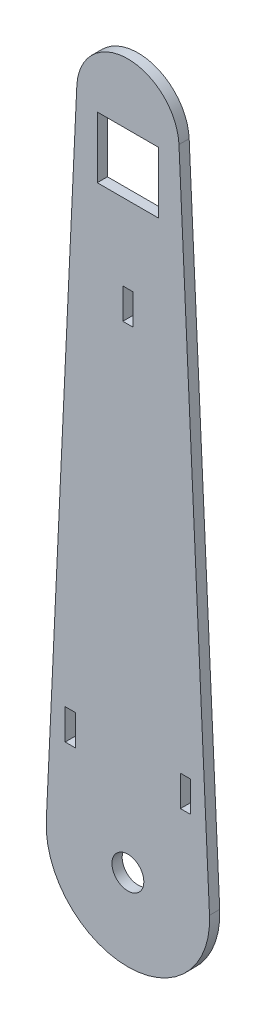
SolidWorks part; units mm, degrees
ref_plane "Front Plane" through (0, 0, 0) normal (0, 0, 1) x (1, 0, 0)
ref_plane "Top Plane" through (0, 0, 0) normal (0, 1, 0) x (1, 0, 0)
ref_plane "Right Plane" through (0, 0, 0) normal (1, 0, 0) x (0, 0, -1)
sketch "Sketch1" plane through (0, 0, 0) normal (0, 0, 1) x (1, 0, 0)
  line L0 (-25.3722, 1.1884) -> (-15.875, 203.9436)
  line L1 (25.3722, 1.1884) -> (15.875, 203.9436)
  line L19 (-19.5072, 34.925) -> (-16.3322, 34.925)
  line L20 (-19.5072, 34.925) -> (-19.5072, 25.4)
  line L21 (-19.5072, 25.4) -> (-16.3322, 25.4)
  line L22 (-16.3322, 34.925) -> (-16.3322, 25.4)
  line L23 (-1.5875, 147.6375) -> (1.5875, 147.6375)
  line L24 (-1.5875, 147.6375) -> (-1.5875, 157.1625)
  line L25 (-1.5875, 157.1625) -> (1.5875, 157.1625)
  line L26 (1.5875, 147.6375) -> (1.5875, 157.1625)
  line L27 (-1.5875, 147.6375) -> (1.5875, 157.1625) construction
  line L28 (-1.5875, 157.1625) -> (1.5875, 147.6375) construction
  line L29 (16.3322, 25.4) -> (19.5072, 25.4)
  line L30 (16.3322, 25.4) -> (16.3322, 34.925)
  line L31 (16.3322, 34.925) -> (19.5072, 34.925)
  line L32 (19.5072, 25.4) -> (19.5072, 34.925)
  line L33 (-9.525, 180.975) -> (9.525, 180.975)
  line L34 (-9.525, 180.975) -> (-9.525, 200.025)
  line L35 (-9.525, 200.025) -> (9.525, 200.025)
  line L36 (9.525, 180.975) -> (9.525, 200.025)
  line L37 (-9.525, 180.975) -> (9.525, 200.025) construction
  line L38 (-9.525, 200.025) -> (9.525, 180.975) construction
  circle A0 centre (0, 0) radius 4.953
  arc A1 (25.3722, 1.1884) -> (-25.3722, 1.1884) centre (0, 0) cw
  arc A2 (-15.875, 203.9436) -> (15.875, 203.9436) centre (0, 203.2) cw
  point P12 (0, 152.4)
  point P16 (0, 190.5)
  point P26 (0, 197.7179)
  point P27 (0, 0)
  point P28 (0, 200.025)
  dimension "D1" = 9.906
  dimension "D2" = 25.4
  dimension "D5" = 19.05
  dimension "D3" = 31.75
  dimension "D4" = 203.2
  dimension "D6" = 3.175
  dimension "D7" = 16.3322
  dimension "D8" = 9.525
  dimension "D9" = 25.4
  dimension "D10" = 50.8
  dimension "D11" = 16.3322
  dimension "D12" = 12.7
extrude "Boss-Extrude1" add sketch "Sketch1" along normal blind 3.175
